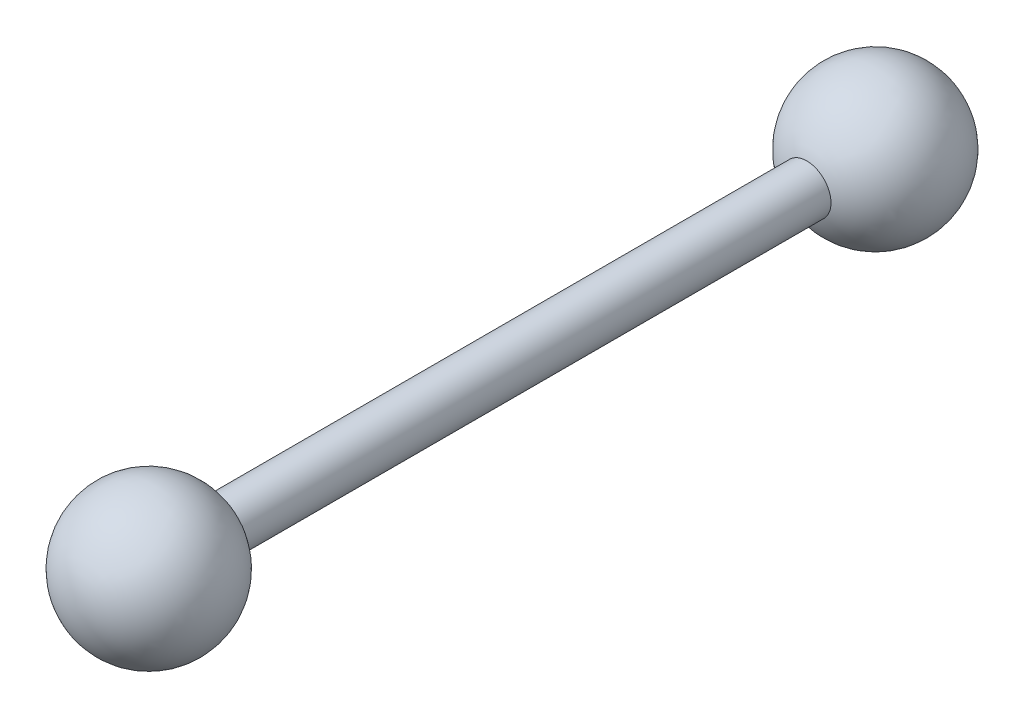
SolidWorks part; units mm, degrees
ref_plane "Front Plane" through (0, 0, 0) normal (0, 0, 1) x (1, 0, 0)
ref_plane "Top Plane" through (0, 0, 0) normal (0, 1, 0) x (1, 0, 0)
ref_plane "Right Plane" through (0, 0, 0) normal (1, 0, 0) x (0, 0, -1)
sketch "Sketch1" plane through (0, 0, 0) normal (0, 1, 0) x (1, 0, 0)
  line L0 (0, 90) -> (0, -90)
  line L1 (5, 60.8579) -> (5, -60.8579)
  arc A0 (5, 60.8579) -> (0, 90) centre (0, 75) ccw
  arc A1 (0, -90) -> (5, -60.8579) centre (0, -75) ccw
  point P6 (0, 0)
  dimension "D3" = 30
  dimension "D1" = 150
  dimension "D2" = 5
revolve "Revolve1" add sketch "Sketch1" angle 360 about L0
